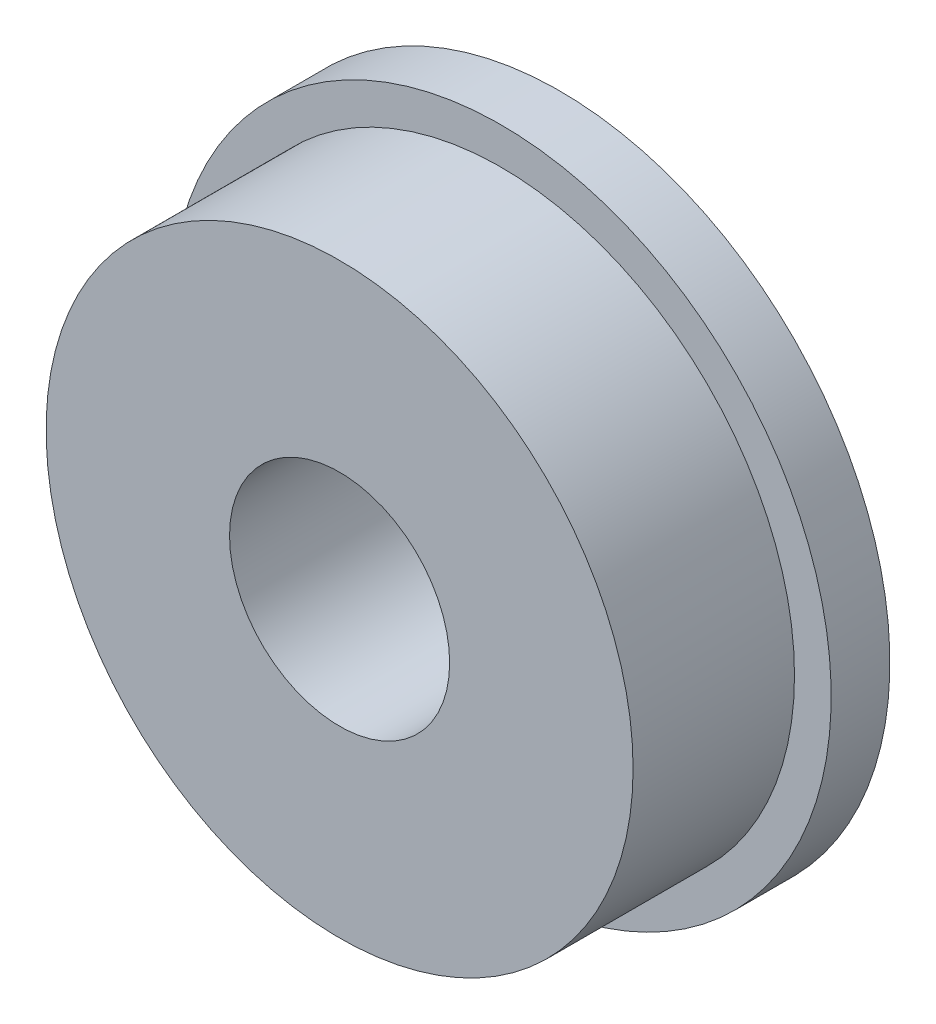
SolidWorks part; units mm, degrees
material "不锈钢 (铁素体)"
ref_plane "前视基准面" through (0, 0, 0) normal (0, 0, 1) x (1, 0, 0)
ref_plane "上视基准面" through (0, 0, 0) normal (0, 1, 0) x (1, 0, 0)
ref_plane "右视基准面" through (0, 0, 0) normal (1, 0, 0) x (0, 0, -1)
sketch "草图1" plane through (0, 0, 0) normal (0, 0, 1) x (1, 0, 0)
  circle A0 centre (0, 0) radius 4
extrude "凸台-拉伸1" add sketch "草图1" along normal blind 2.2
sketch "草图2" plane through (0, 0, 2.2) normal (0, 0, 1) x (1, 0, 0)
  circle A0 centre (0, 0) radius 1.5
extrude "切除-拉伸1" cut sketch "草图2" against normal blind 7
sketch "草图3" plane through (0, 0, 0) normal (0, 0, -1) x (-1, 0, 0)
  circle A0 centre (0, 0) radius 4.5
extrude "凸台-拉伸2" add sketch "草图3" along normal blind 0.8
sketch "草图4" plane through (0, 0, 0) normal (0, 0, 1) x (1, 0, 0)
  circle A0 centre (0, 0) radius 1.5
extrude "切除-拉伸2" cut sketch "草图4" against normal blind 0.8
